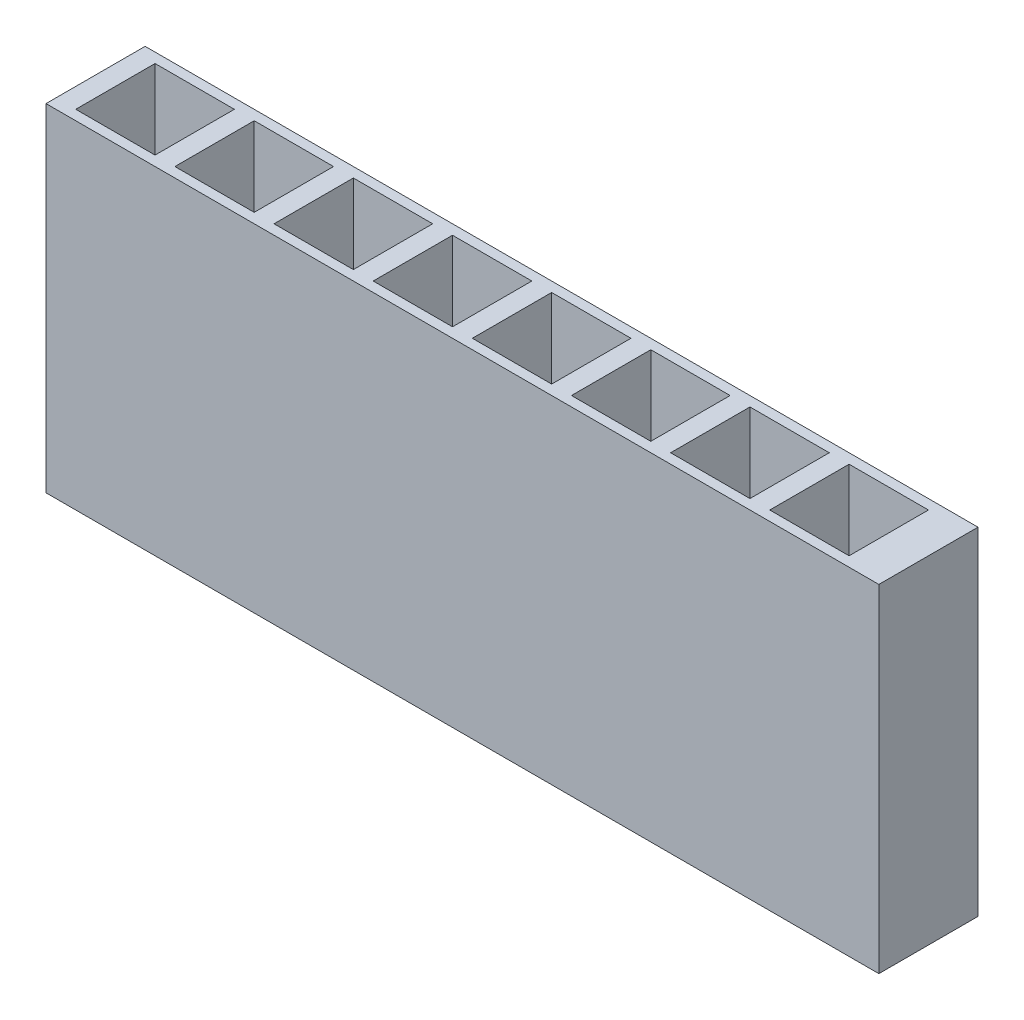
SolidWorks part; units mm, degrees
material "ABS"
ref_plane "Front Plane" through (0, 0, 0) normal (0, 0, 1) x (1, 0, 0)
ref_plane "Top Plane" through (0, 0, 0) normal (0, 1, 0) x (1, 0, 0)
ref_plane "Right Plane" through (0, 0, 0) normal (1, 0, 0) x (0, 0, -1)
sketch "Sketch1" plane through (0, 0, 0) normal (0, 1, 0) x (1, 0, 0)
  line L1 (-10.5, 1.25) -> (10.5, 1.25)
  line L2 (-10.5, 1.25) -> (-10.5, -1.25)
  line L3 (-10.5, -1.25) -> (10.5, -1.25)
  line L4 (10.5, 1.25) -> (10.5, -1.25)
  line L5 (-10.5, 1.25) -> (10.5, -1.25) construction
  line L6 (-10.5, -1.25) -> (10.5, 1.25) construction
  point P0 (0, 0)
  dimension "D1" = 21
  dimension "D2" = 2.5
extrude "Boss-Extrude1" add sketch "Sketch1" along normal blind 8.5
sketch "Sketch2" plane through (0, 8.5, 0) normal (0, 1, 0) x (1, 0, 0)
  line L0 (-10.5, 0) -> (0, 0) construction
  line L1 (-10.5, 1.25) -> (-10.5, -1.25) construction
  line L2 (-7.5, 1) -> (-5.5, 1)
  line L3 (-10, 1) -> (-8, 1)
  line L4 (-10, 1) -> (-10, -1)
  line L5 (-10, -1) -> (-8, -1)
  line L6 (-8, 1) -> (-8, -1)
  line L7 (-10, 1) -> (-8, -1) construction
  line L8 (-10, -1) -> (-8, 1) construction
  line L9 (-7.5, 1) -> (-7.5, -1)
  line L10 (-5.5, 1) -> (-5.5, -1)
  line L11 (-7.5, -1) -> (-5.5, -1)
  line L12 (-5, 1) -> (-3, 1)
  line L13 (-5, 1) -> (-5, -1)
  line L14 (-3, 1) -> (-3, -1)
  line L15 (-5, -1) -> (-3, -1)
  line L16 (-2.5, 1) -> (-0.5, 1)
  line L17 (-2.5, 1) -> (-2.5, -1)
  line L18 (-0.5, 1) -> (-0.5, -1)
  line L19 (-2.5, -1) -> (-0.5, -1)
  line L20 (0, 1) -> (2, 1)
  line L21 (0, 1) -> (0, -1)
  line L22 (2, 1) -> (2, -1)
  line L23 (0, -1) -> (2, -1)
  line L24 (2.5, 1) -> (4.5, 1)
  line L25 (2.5, 1) -> (2.5, -1)
  line L26 (4.5, 1) -> (4.5, -1)
  line L27 (2.5, -1) -> (4.5, -1)
  line L28 (5, 1) -> (7, 1)
  line L29 (5, 1) -> (5, -1)
  line L30 (7, 1) -> (7, -1)
  line L31 (5, -1) -> (7, -1)
  line L32 (7.5, 1) -> (9.5, 1)
  line L33 (7.5, 1) -> (7.5, -1)
  line L34 (9.5, 1) -> (9.5, -1)
  line L35 (7.5, -1) -> (9.5, -1)
  point P5 (-9, 0)
  dimension "D1" = 2
  dimension "D2" = 2
  dimension "D3" = 1.5
  dimension "D4" = 8
extrude "Cut-Extrude1" cut sketch "Sketch2" against normal blind 5
